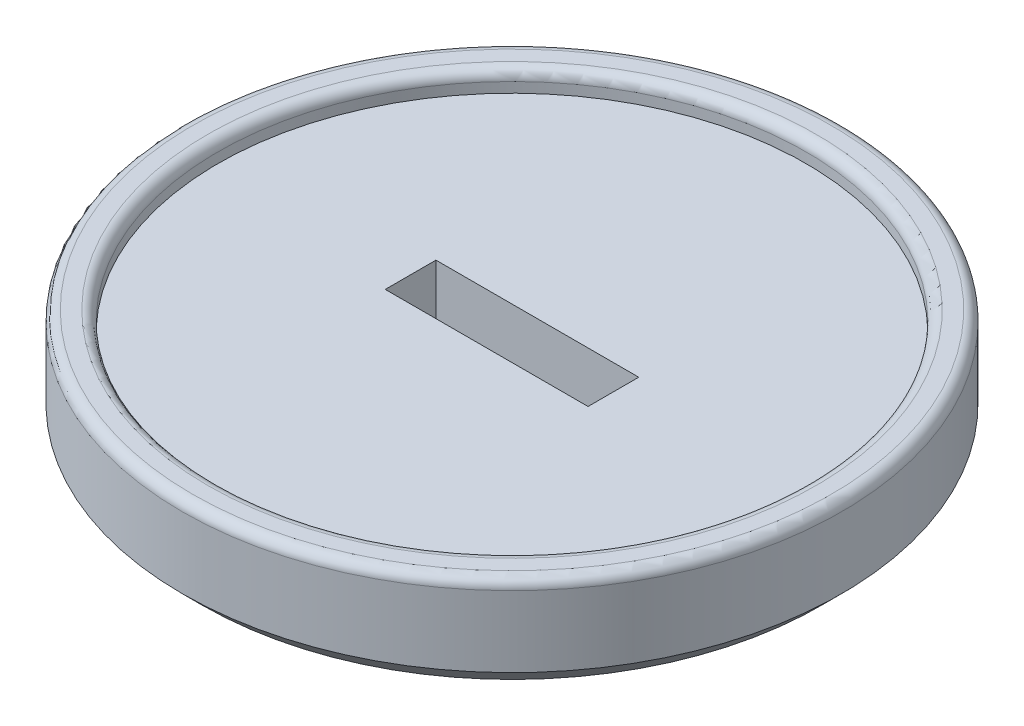
SolidWorks part; units mm, degrees
ref_plane "Alzado" through (0, 0, 0) normal (0, 0, 1) x (1, 0, 0)
ref_plane "Planta" through (0, 0, 0) normal (0, 1, 0) x (1, 0, 0)
ref_plane "Vista lateral" through (0, 0, 0) normal (1, 0, 0) x (0, 0, -1)
sketch "Sketch1" plane through (0, 0, 0) normal (0, 1, 0) x (1, 0, 0)
  circle A0 centre (0, 0) radius 32.5
  dimension "D1" = 65
extrude "Boss-Extrude4" add sketch "Sketch1" along normal blind 10 contours A0
sketch "Sketch4" plane through (0, 10, 0) normal (0, 1, 0) x (1, 0, 0)
  line L1 (-10, 2.5) -> (10, 2.5)
  line L2 (-10, 2.5) -> (-10, -2.5)
  line L3 (-10, -2.5) -> (10, -2.5)
  line L4 (10, 2.5) -> (10, -2.5)
  line L5 (-10, 2.5) -> (10, -2.5) construction
  line L6 (-10, -2.5) -> (10, 2.5) construction
  point P0 (0, 0)
  dimension "D1" = 20
  dimension "D2" = 5
extrude "Cut-Extrude1" cut sketch "Sketch4" against normal up to next
sketch "Sketch5" plane through (0, 10, 0) normal (0, 1, 0) x (1, 0, 0)
  circle A0 centre (0, 0) radius 29
  dimension "D1" = 58
extrude "Cut-Extrude3" cut sketch "Sketch5" against normal blind 2
fillet "Fillet1" radius 1 1 edges at (0, 10, 32.5)
fillet "Fillet2" radius 1 1 edges at (0, 10, 29)
chamfer "Chamfer1" distance 2 angle 45 1 edges at (0, 0, 32.5)
